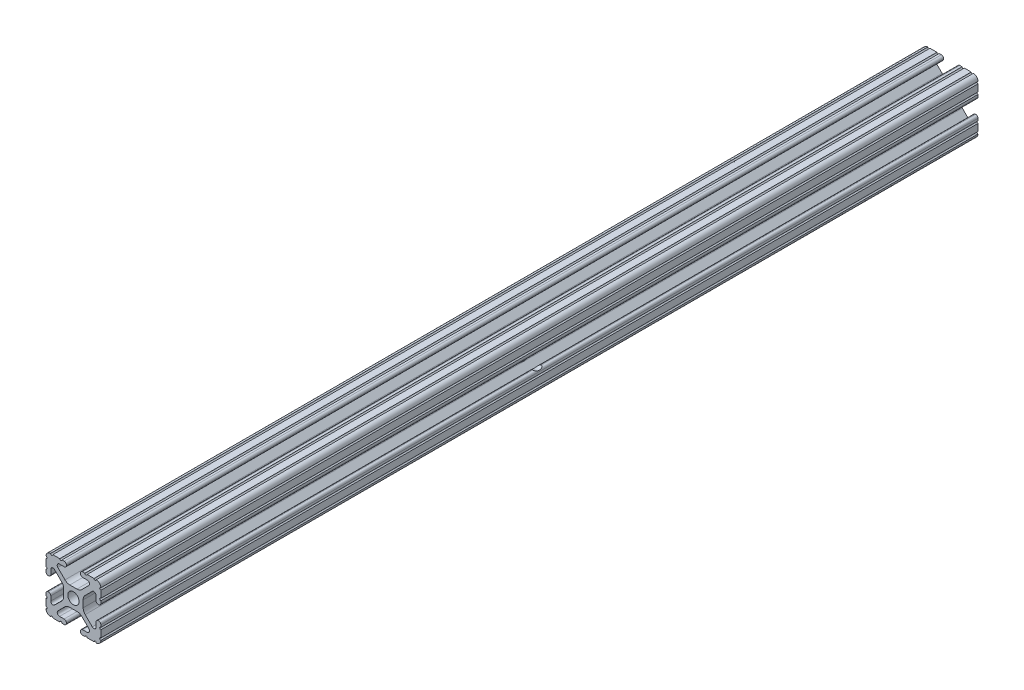
SolidWorks part; units mm, degrees
ref_plane "Front Plane" through (0, 0, 0) normal (0, 0, 1) x (1, 0, 0)
ref_plane "Top Plane" through (0, 0, 0) normal (0, 1, 0) x (1, 0, 0)
ref_plane "Right Plane" through (0, 0, 0) normal (1, 0, 0) x (0, 0, -1)
sketch "Sketch1" plane through (0, 0, 0) normal (0, 0, 1) x (1, 0, 0)
  line L88 (-7.1797, -8.6452) -> (-3.9523, -5.4237)
  line L89 (-1.7093, -4.4958) -> (1.7093, -4.4958)
  line L90 (3.9523, -5.4237) -> (7.1797, -8.6452)
  line L91 (6.4164, -10.4902) -> (4.2875, -10.4902)
  line L92 (3.2385, -11.5392) -> (3.2385, -11.651)
  line L93 (4.2875, -12.7) -> (5.3171, -12.7)
  line L94 (6.3331, -12.7) -> (9.5504, -12.7)
  line L95 (12.7, -9.5504) -> (12.7, -6.3331)
  line L96 (12.7, -5.3171) -> (12.7, -4.2875)
  line L97 (11.651, -3.2385) -> (11.5392, -3.2385)
  line L98 (10.4902, -4.2875) -> (10.4902, -6.4021)
  line L99 (8.7371, -7.1294) -> (5.441, -3.8408)
  line L100 (4.5085, -1.5932) -> (4.5085, 1.5932)
  line L101 (5.441, 3.8408) -> (8.7371, 7.1294)
  line L102 (10.4902, 6.4021) -> (10.4902, 4.2875)
  line L103 (11.5392, 3.2385) -> (11.651, 3.2385)
  line L104 (12.7, 4.2875) -> (12.7, 5.3171)
  line L105 (12.7, 6.3331) -> (12.7, 9.5504)
  line L106 (9.5504, 12.7) -> (6.3331, 12.7)
  line L107 (5.3171, 12.7) -> (4.2875, 12.7)
  line L108 (3.2385, 11.651) -> (3.2385, 11.5392)
  line L109 (4.2875, 10.4902) -> (6.4768, 10.4902)
  line L110 (7.207, 8.7244) -> (3.8983, 5.4232)
  line L111 (1.6558, 4.4958) -> (-1.6558, 4.4958)
  line L112 (-3.8983, 5.4232) -> (-7.207, 8.7244)
  line L113 (-6.4768, 10.4902) -> (-4.2875, 10.4902)
  line L114 (-3.2385, 11.5392) -> (-3.2385, 11.651)
  line L115 (-4.2875, 12.7) -> (-5.3171, 12.7)
  line L116 (-6.3331, 12.7) -> (-9.5504, 12.7)
  line L117 (-12.7, 9.5504) -> (-12.7, 6.3331)
  line L118 (-12.7, 5.3171) -> (-12.7, 4.2875)
  line L119 (-11.651, 3.2385) -> (-11.5392, 3.2385)
  line L120 (-10.4902, 4.2875) -> (-10.4902, 6.4021)
  line L121 (-8.7371, 7.1294) -> (-5.441, 3.8408)
  line L122 (-4.5085, 1.5932) -> (-4.5085, -1.5932)
  line L123 (-5.441, -3.8408) -> (-8.7371, -7.1294)
  line L124 (-10.4902, -6.4021) -> (-10.4902, -4.2875)
  line L125 (-11.5392, -3.2385) -> (-11.651, -3.2385)
  line L126 (-12.7, -4.2875) -> (-12.7, -5.3171)
  line L127 (-12.7, -6.3331) -> (-12.7, -9.5504)
  line L128 (-9.5504, -12.7) -> (-6.3331, -12.7)
  line L129 (-5.3171, -12.7) -> (-4.2875, -12.7)
  line L130 (-3.2385, -11.651) -> (-3.2385, -11.5392)
  line L131 (-4.2875, -10.4902) -> (-6.4164, -10.4902)
  circle A1 centre (0, 0) radius 2.6035
  arc A104 (-7.1797, -8.6452) -> (-6.4164, -10.4902) centre (-6.4164, -9.4098) ccw
  arc A105 (-1.7093, -4.4958) -> (-3.9523, -5.4237) centre (-1.7093, -7.6708) ccw
  arc A106 (3.9523, -5.4237) -> (1.7093, -4.4958) centre (1.7093, -7.6708) ccw
  arc A107 (6.4164, -10.4902) -> (7.1797, -8.6452) centre (6.4164, -9.4098) ccw
  arc A108 (4.2875, -10.4902) -> (3.2385, -11.5392) centre (4.2875, -11.5392) ccw
  arc A109 (3.2385, -11.651) -> (4.2875, -12.7) centre (4.2875, -11.651) ccw
  arc A110 (6.3331, -12.7) -> (5.3171, -12.7) centre (5.8251, -12.7) ccw
  arc A111 (10.5664, -12.6998) -> (9.5504, -12.7) centre (10.0584, -12.7) ccw
  arc A112 (10.5664, -12.6998) -> (12.6998, -10.5664) centre (10.5918, -10.5918) ccw
  arc A113 (12.7, -9.5504) -> (12.6998, -10.5664) centre (12.7, -10.0584) ccw
  arc A114 (12.7, -5.3171) -> (12.7, -6.3331) centre (12.7, -5.8251) ccw
  arc A115 (12.7, -4.2875) -> (11.651, -3.2385) centre (11.651, -4.2875) ccw
  arc A116 (11.5392, -3.2385) -> (10.4902, -4.2875) centre (11.5392, -4.2875) ccw
  arc A117 (8.7371, -7.1294) -> (10.4902, -6.4021) centre (9.4628, -6.4021) ccw
  arc A118 (4.5085, -1.5932) -> (5.441, -3.8408) centre (7.6835, -1.5932) ccw
  arc A119 (5.441, 3.8408) -> (4.5085, 1.5932) centre (7.6835, 1.5932) ccw
  arc A120 (10.4902, 6.4021) -> (8.7371, 7.1294) centre (9.4628, 6.4021) ccw
  arc A121 (10.4902, 4.2875) -> (11.5392, 3.2385) centre (11.5392, 4.2875) ccw
  arc A122 (11.651, 3.2385) -> (12.7, 4.2875) centre (11.651, 4.2875) ccw
  arc A123 (12.7, 6.3331) -> (12.7, 5.3171) centre (12.7, 5.8251) ccw
  arc A124 (12.6998, 10.5664) -> (12.7, 9.5504) centre (12.7, 10.0584) ccw
  arc A125 (12.6998, 10.5664) -> (10.5664, 12.6998) centre (10.5918, 10.5918) ccw
  arc A126 (9.5504, 12.7) -> (10.5664, 12.6998) centre (10.0584, 12.7) ccw
  arc A127 (5.3171, 12.7) -> (6.3331, 12.7) centre (5.8251, 12.7) ccw
  arc A128 (4.2875, 12.7) -> (3.2385, 11.651) centre (4.2875, 11.651) ccw
  arc A129 (3.2385, 11.5392) -> (4.2875, 10.4902) centre (4.2875, 11.5392) ccw
  arc A130 (7.207, 8.7244) -> (6.4768, 10.4902) centre (6.4768, 9.4563) ccw
  arc A131 (1.6558, 4.4958) -> (3.8983, 5.4232) centre (1.6558, 7.6708) ccw
  arc A132 (-3.8983, 5.4232) -> (-1.6558, 4.4958) centre (-1.6558, 7.6708) ccw
  arc A133 (-6.4768, 10.4902) -> (-7.207, 8.7244) centre (-6.4768, 9.4563) ccw
  arc A134 (-4.2875, 10.4902) -> (-3.2385, 11.5392) centre (-4.2875, 11.5392) ccw
  arc A135 (-3.2385, 11.651) -> (-4.2875, 12.7) centre (-4.2875, 11.651) ccw
  arc A136 (-6.3331, 12.7) -> (-5.3171, 12.7) centre (-5.8251, 12.7) ccw
  arc A137 (-10.5664, 12.6998) -> (-9.5504, 12.7) centre (-10.0584, 12.7) ccw
  arc A138 (-10.5664, 12.6998) -> (-12.6998, 10.5664) centre (-10.5918, 10.5918) ccw
  arc A139 (-12.7, 9.5504) -> (-12.6998, 10.5664) centre (-12.7, 10.0584) ccw
  arc A140 (-12.7, 5.3171) -> (-12.7, 6.3331) centre (-12.7, 5.8251) ccw
  arc A141 (-12.7, 4.2875) -> (-11.651, 3.2385) centre (-11.651, 4.2875) ccw
  arc A142 (-11.5392, 3.2385) -> (-10.4902, 4.2875) centre (-11.5392, 4.2875) ccw
  arc A143 (-8.7371, 7.1294) -> (-10.4902, 6.4021) centre (-9.4628, 6.4021) ccw
  arc A144 (-4.5085, 1.5932) -> (-5.441, 3.8408) centre (-7.6835, 1.5932) ccw
  arc A145 (-5.441, -3.8408) -> (-4.5085, -1.5932) centre (-7.6835, -1.5932) ccw
  arc A146 (-10.4902, -6.4021) -> (-8.7371, -7.1294) centre (-9.4628, -6.4021) ccw
  arc A147 (-10.4902, -4.2875) -> (-11.5392, -3.2385) centre (-11.5392, -4.2875) ccw
  arc A148 (-11.651, -3.2385) -> (-12.7, -4.2875) centre (-11.651, -4.2875) ccw
  arc A149 (-12.7, -6.3331) -> (-12.7, -5.3171) centre (-12.7, -5.8251) ccw
  arc A150 (-12.6998, -10.5664) -> (-12.7, -9.5504) centre (-12.7, -10.0584) ccw
  arc A151 (-12.6998, -10.5664) -> (-10.5664, -12.6998) centre (-10.5918, -10.5918) ccw
  arc A152 (-9.5504, -12.7) -> (-10.5664, -12.6998) centre (-10.0584, -12.7) ccw
  arc A153 (-5.3171, -12.7) -> (-6.3331, -12.7) centre (-5.8251, -12.7) ccw
  arc A154 (-4.2875, -12.7) -> (-3.2385, -11.651) centre (-4.2875, -11.651) ccw
  arc A155 (-3.2385, -11.5392) -> (-4.2875, -10.4902) centre (-4.2875, -11.5392) ccw
extrude "Boss-Extrude1" add sketch "Sketch1" along normal mid plane 406.4
sketch "Sketch2" plane through (-12.7, 0, 0) normal (-1, 0, 0) x (0, 0, 1)
  circle A0 centre (0, 0) radius 3.81
  dimension "D1" = 7.62
extrude "Cut-Extrude1" cut sketch "Sketch2" against normal blind 25.4
sketch "Sketch3" plane through (0, 4.4958, 0) normal (0, 1, 0) x (1, 0, 0)
  line L0 (0, 219.8063) -> (0, -211.9937) construction
  line L3 (0, 0) -> (42.3686, 0) construction
  line L4 (1.6558, -203.2) -> (-1.6558, -203.2) construction
  circle A0 centre (0, -190.5) radius 3.175
  circle A1 centre (0, 190.5) radius 3.175
  dimension "D1" = 6.35
  dimension "D2" = 12.7
extrude "Cut-Extrude2" cut sketch "Sketch3" against normal through all both and the other way through all
